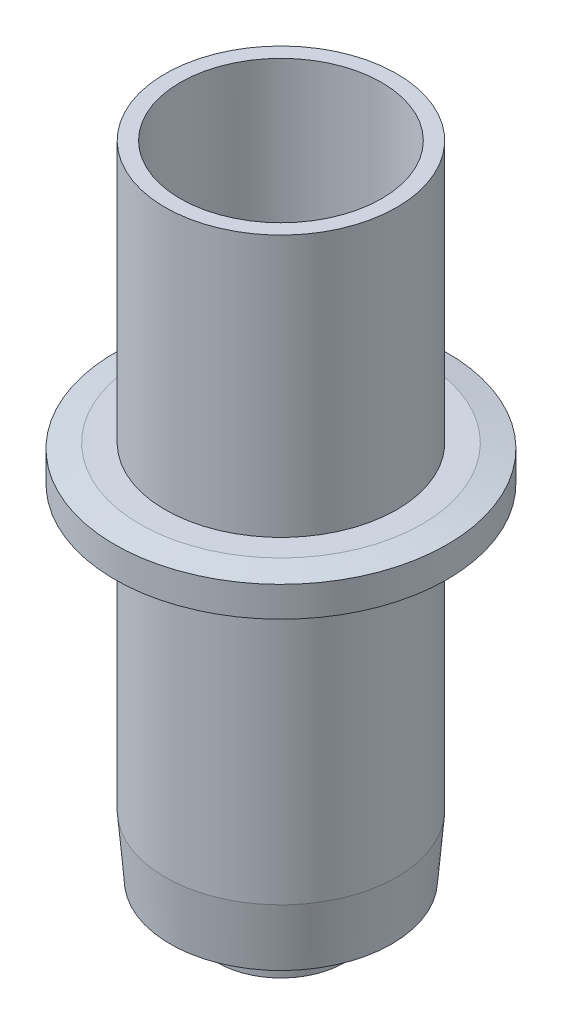
SolidWorks part; units mm, degrees
ref_plane "Front Plane" through (0, 0, 0) normal (0, 0, 1) x (1, 0, 0)
ref_plane "Top Plane" through (0, 0, 0) normal (0, 1, 0) x (1, 0, 0)
ref_plane "Right Plane" through (0, 0, 0) normal (1, 0, 0) x (0, 0, -1)
sketch "Sketch1" plane through (0, 0, 0) normal (0, 0, 1) x (1, 0, 0)
  line L0 (0, -143.9505) -> (0, 7053.5726) construction
  line L1 (0, 0) -> (3, 0)
  line L2 (3, 0) -> (3.2, 5.5)
  line L4 (3.2, 5.5) -> (5.5, 5.5)
  line L5 (5.5, 5.5) -> (5.75, 8.5)
  line L6 (5.75, 8.5) -> (5.75, 22.3)
  line L7 (5.75, 22.3) -> (7, 22.3)
  line L8 (7, 22.3) -> (8.25, 22.55)
  line L9 (8.25, 22.55) -> (8.25, 24.05)
  line L10 (8.25, 24.05) -> (7, 24.3)
  line L11 (7, 24.3) -> (5.75, 24.3)
  line L12 (5.75, 24.3) -> (5.75, 37.3)
  line L13 (5.75, 37.3) -> (0, 37.3)
  line L14 (0, 37.3) -> (0, 0)
  point P18 (0, 37.3)
  point P29 (0, 0)
  dimension "D2" = 22.3
  dimension "D3" = 11.5
  dimension "D4" = 2
  dimension "D5" = 1.5
  dimension "D6" = 16.5
  dimension "D7" = 5.5
  dimension "D8" = 3.2
  dimension "D10" = 6
  dimension "D11" = 8.5
  dimension "D12" = 1.25
  dimension "D13" = 13
  dimension "D14" = 11
revolve "5.63 mm bottom to pen tip" add sketch "Sketch1" angle 360 about L0
sketch "Sketch2" plane through (0, 0, 0) normal (1, 0, 0) x (0, 0, -1)
  line L0 (0.75, -5.63) -> (0.75, -0.43)
  line L1 (0.75, -0.43) -> (2.575, -0.43)
  line L2 (2.575, -0.43) -> (2.575, 6.87)
  line L3 (2.575, 6.87) -> (5, 6.87)
  line L4 (5, 6.87) -> (5, 39.1622)
  line L5 (0, -1000) -> (0, 49000) construction
  line L6 (5, 39.1622) -> (0, 39.1622)
  line L7 (0.75, -5.63) -> (0, -5.63)
  line L8 (-3, 0) -> (3, 0) construction
  line L9 (0, 39.1622) -> (0, -5.63)
  dimension "D1" = 5.63
  dimension "D2" = 1.5
  dimension "D3" = 5.15
  dimension "D4" = 10
  dimension "D5" = 5.2
  dimension "D6" = 12.5
revolve "Cut-Revolve1" cut sketch "Sketch2" angle 360 about L5
ref_plane "Plane1" through (0, 0, 0) normal (0, -1, 0) x (-1, 0, 0)
sketch "Sketch3" plane through (0, 0, 0) normal (0, -1, 0) x (-1, 0, 0)
  circle A0 centre (0, 0) radius 4.0878
extrude "Cut-Extrude1" cut sketch "Sketch3" against normal offset from surface (3.5 mm away) 2 up to face at (5.5, 5.5, 0)
